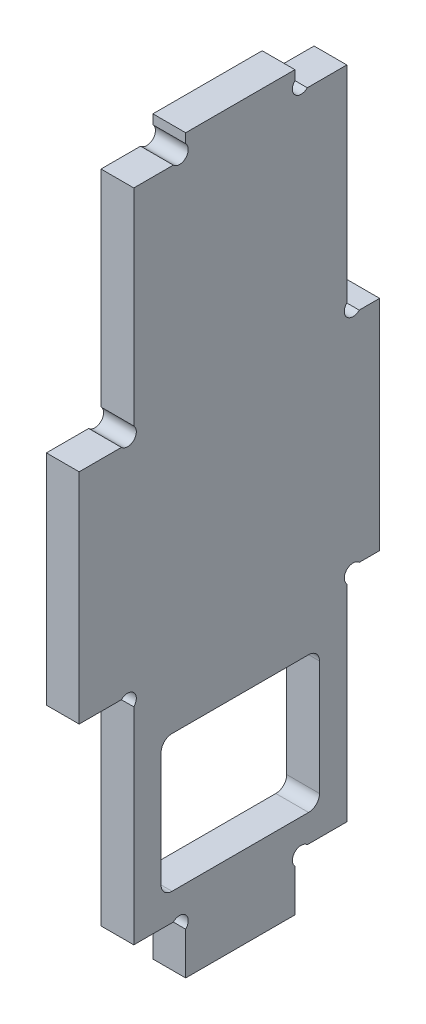
SolidWorks part; units mm, degrees
ref_plane "Plan de face" through (0, 0, 0) normal (0, 0, 1) x (1, 0, 0)
ref_plane "Plan de dessus" through (0, 0, 0) normal (0, 1, 0) x (1, 0, 0)
ref_plane "Plan de droite" through (0, 0, 0) normal (1, 0, 0) x (0, 0, -1)
sketch "Esquisse1" plane through (0, 0, 0) normal (1, 0, 0) x (0, 0, -1)
  line L13 (19.5, 7.7373) -> (19.5, 0)
  line L15 (17.2373, 10) -> (10, 10)
  line L17 (51.2627, 50) -> (55, 50)
  line L18 (7.7373, 50) -> (0, 50)
  line L19 (39.5, 7.7373) -> (39.5, 0)
  line L20 (51.2627, 90) -> (55, 90)
  line L21 (7.7373, 90) -> (0, 90)
  line L22 (19.5, 0) -> (39.5, 0)
  line L23 (41.7627, 10) -> (49, 10)
  line L24 (49, 10) -> (49, 47.7373)
  line L25 (10, 10) -> (10, 47.7373)
  line L26 (55, 90) -> (55, 50)
  line L27 (0, 50) -> (0, 90)
  line L29 (19.5, 132.2627) -> (19.5, 134)
  line L30 (39.5, 132.2627) -> (39.5, 134)
  line L31 (10, 92.2627) -> (10, 130)
  line L32 (10, 130) -> (17.2373, 130)
  line L33 (19.5, 134) -> (39.5, 134)
  line L34 (41.7627, 130) -> (49, 130)
  line L35 (49, 130) -> (49, 92.2627)
  arc A0 (51.2627, 50) -> (49, 47.7373) centre (50.1314, 48.8686) ccw
  arc A1 (10, 47.7373) -> (7.7373, 50) centre (8.8686, 48.8686) ccw
  arc A2 (19.5, 7.7373) -> (17.2373, 10) centre (18.3686, 8.8686) ccw
  arc A3 (39.5, 7.7373) -> (41.7627, 10) centre (40.6314, 8.8686) cw
  arc A4 (10, 92.2627) -> (7.7373, 90) centre (8.8686, 91.1314) cw
  arc A5 (51.2627, 90) -> (49, 92.2627) centre (50.1314, 91.1314) cw
  arc A6 (17.2373, 130) -> (19.5, 132.2627) centre (18.3686, 131.1314) ccw
  arc A7 (41.7627, 130) -> (39.5, 132.2627) centre (40.6314, 131.1314) cw
  point P1 (13.6186, 10)
  dimension "D14" = 1.1314
  dimension "D15" = 1.1314
  dimension "D17" = 1.1314
  dimension "D23" = 1.1314
  dimension "D10" = 1.6
  dimension "D1" = 6
  dimension "D2" = 10
  dimension "D3" = 9.5
  dimension "D4" = 9.5
  dimension "D5" = 10
  dimension "D6" = 40
  dimension "D7" = 40
  dimension "D8" = 40
  dimension "D9" = 4
  dimension "D11" = 1.1314
  dimension "D12" = 1.1314
  dimension "D13" = 1.1314
  dimension "D16" = 20
  dimension "D18" = 1.1314
  dimension "D19" = 1.1314
  dimension "D20" = 1.1314
  dimension "D21" = 1.1314
  dimension "D22" = 1.1314
  dimension "D24" = 3.7373
  dimension "D25" = 1.7373
  dimension "D26" = 1.1314
  dimension "D27" = 7.2373
  dimension "D28" = 1.1314
  dimension "D29" = 1.7373
  dimension "D30" = 20
  dimension "D31" = 39
  dimension "D32" = 39
extrude "Extrusion1" add sketch "Esquisse1" along normal blind 6
sketch "Esquisse2" plane through (6, 0, 0) normal (1, 0, 0) x (0, 0, -1)
  line L0 (10, 47.7373) -> (10, 10) construction
  line L1 (15, 15) -> (44, 15)
  line L2 (15, 15) -> (15, 40)
  line L3 (15, 40) -> (44, 40)
  line L4 (44, 15) -> (44, 40)
  line L5 (49, 10) -> (49, 47.7373) construction
  line L6 (10, 10) -> (17.2373, 10) construction
  dimension "D1" = 5
  dimension "D2" = 5
  dimension "D3" = 5
  dimension "D4" = 25
extrude "Enlèv. mat.-Extru.1" cut sketch "Esquisse2" against normal through all
fillet "Congé1" radius 2 4 edges at (3, 15, -44) (3, 15, -15) (3, 40, -15) (3, 40, -44)
